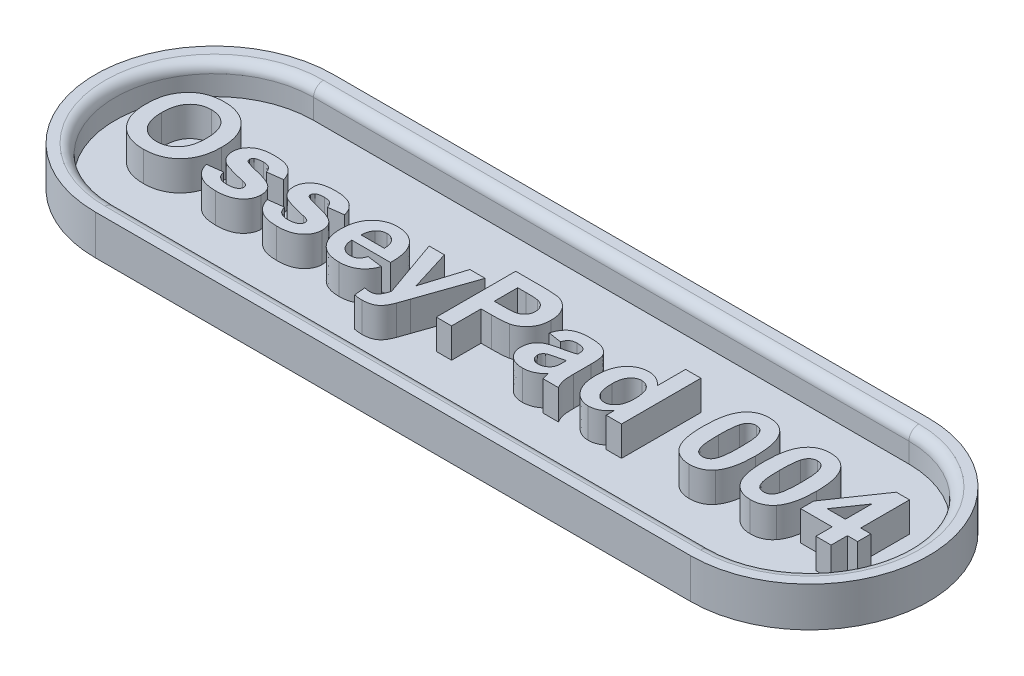
SolidWorks part; units mm, degrees
ref_plane "Front Plane" through (0, 0, 0) normal (0, 0, 1) x (1, 0, 0)
ref_plane "Top Plane" through (0, 0, 0) normal (0, 1, 0) x (1, 0, 0)
ref_plane "Right Plane" through (0, 0, 0) normal (1, 0, 0) x (0, 0, -1)
sketch "Sketch1" plane through (0, 0, 0) normal (0, 1, 0) x (1, 0, 0)
  line L0 (-15, 0) -> (15, 0) construction
  line L1 (-15, 6) -> (15, 6)
  line L2 (-15, -6) -> (15, -6)
  arc A0 (-15, 6) -> (-15, -6) centre (-15, 0) ccw
  arc A1 (15, -6) -> (15, 6) centre (15, 0) ccw
  point P2 (0, 0)
  dimension "D1" = 12
  dimension "D2" = 30
extrude "Boss-Extrude1" add sketch "Sketch1" along normal blind 2
sketch "Sketch2" plane through (0, 2, 0) normal (0, 1, 0) x (1, 0, 0)
  line L0 (-15, 0) -> (15, 0) construction
  line L1 (-15, 5) -> (15, 5)
  line L2 (-15, -5) -> (15, -5)
  arc A0 (-15, 5) -> (-15, -5) centre (-15, 0) ccw
  arc A1 (15, -5) -> (15, 5) centre (15, 0) ccw
  point P2 (0, 0)
  dimension "D1" = 30
  dimension "D2" = 10
extrude "Cut-Extrude1" cut sketch "Sketch2" against normal blind 1.5
sketch "Sketch3" plane through (0, 0.5, 0) normal (0, 1, 0) x (1, 0, 0)
  line L0 (-21, -1.995) -> (21, -1.995) construction
  line L1 (0, -8.7006) -> (0, 6.9821) construction
  line L3 (-15, -5) -> (15, -5) construction
  text T0 "OsseyPad 004" font "Arial" height 4
  dimension "D1" = 3.005
extrude "Boss-Extrude2" add sketch "Sketch3" along normal blind 1.5
fillet "Fillet1" radius 0.5 4 edges at (0, 2, -5) (20, 2, 0) (0, 2, 5) (-20, 2, 0)
